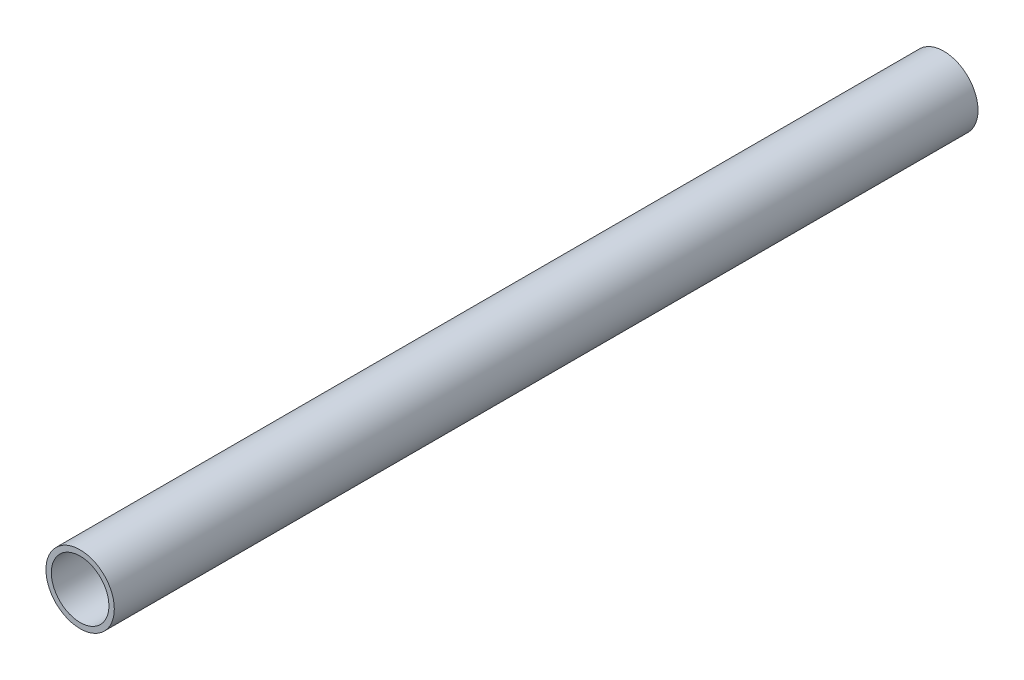
SolidWorks part; units mm, degrees
material "ABS PC"
ref_plane "Front Plane" through (0, 0, 0) normal (0, 0, 1) x (1, 0, 0)
ref_plane "Top Plane" through (0, 0, 0) normal (0, 1, 0) x (1, 0, 0)
ref_plane "Right Plane" through (0, 0, 0) normal (1, 0, 0) x (0, 0, -1)
sketch "Sketch1" plane through (0, 0, 0) normal (0, 0, 1) x (1, 0, 0)
  circle A0 centre (0, 0) radius 12.7
  circle A1 centre (0, 0) radius 15.0812
  dimension "D1" = 30.1625
  dimension "D2" = 25.4
extrude "Boss-Extrude1" add sketch "Sketch1" along normal blind 381
